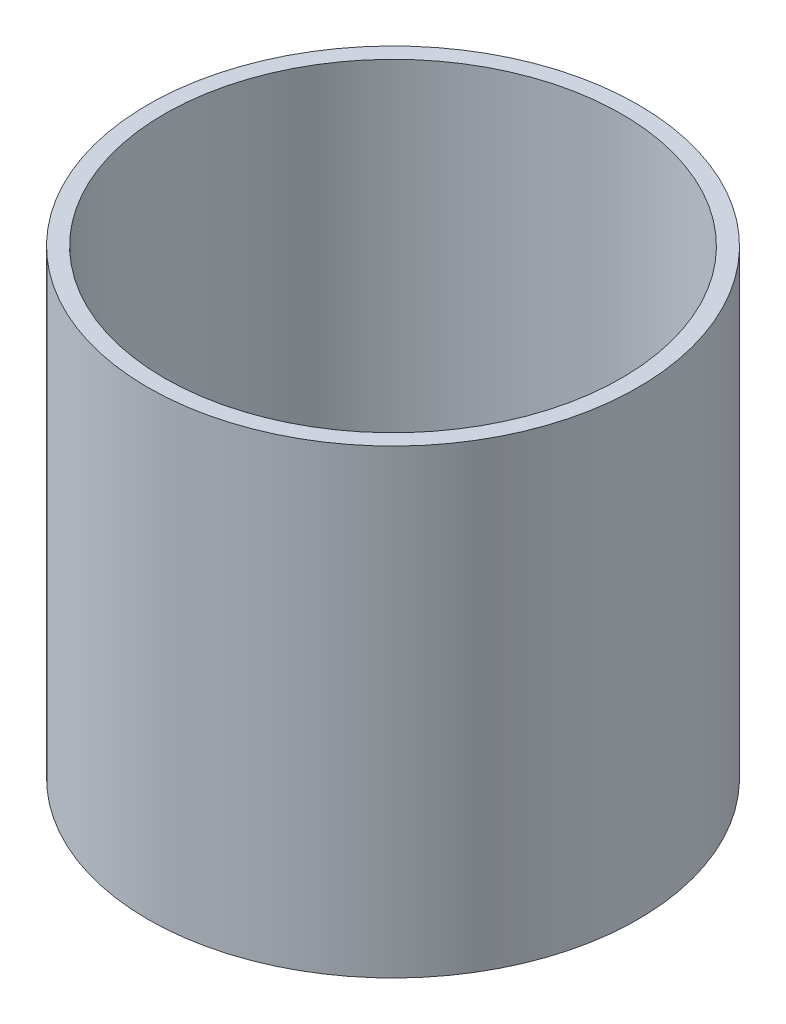
SolidWorks part; units mm, degrees
material "201 Annealed Stainless Steel (SS)"
ref_plane "Front Plane" through (0, 0, 0) normal (0, 0, 1) x (1, 0, 0)
ref_plane "Top Plane" through (0, 0, 0) normal (0, 1, 0) x (1, 0, 0)
ref_plane "Right Plane" through (0, 0, 0) normal (1, 0, 0) x (0, 0, -1)
sketch "Sketch2" plane through (0, 0, 0) normal (0, 1, 0) x (1, 0, 0)
  line L0 (0, 150) -> (0, -150)
  circle A0 centre (0, 0) radius 150
  circle A1 centre (0, 0) radius 140
  dimension "D1" = 300
  dimension "D2" = 280
extrude "Boss-Extrude1" add sketch "Sketch2" along normal blind 282 contours A1 L0 A0 | A1 L0 A0
